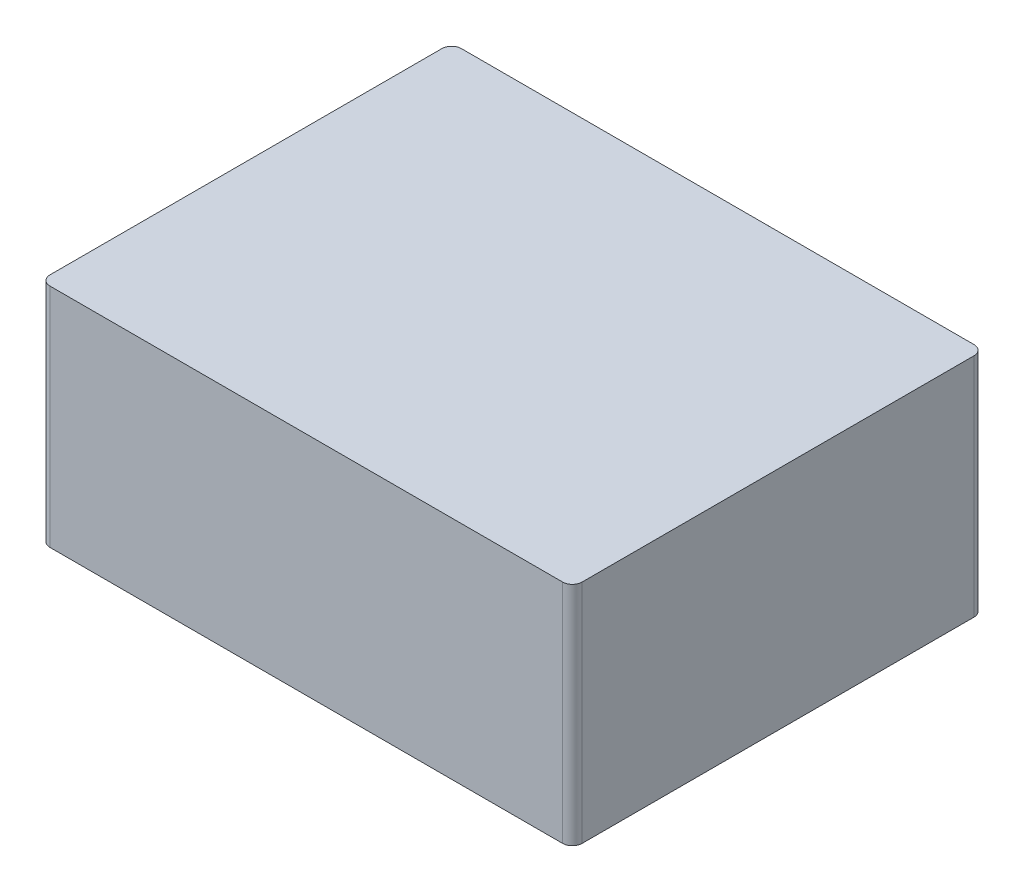
SolidWorks part; units mm, degrees
ref_plane "Front Plane" through (0, 0, 0) normal (0, 0, 1) x (1, 0, 0)
ref_plane "Top Plane" through (0, 0, 0) normal (0, 1, 0) x (1, 0, 0)
ref_plane "Right Plane" through (0, 0, 0) normal (1, 0, 0) x (0, 0, -1)
sketch "Sketch1" plane through (0, 0, 0) normal (0, 1, 0) x (1, 0, 0)
  line L1 (0, 0) -> (109.3, 0)
  line L2 (0, 0) -> (0, 84.5)
  line L3 (0, 84.5) -> (109.3, 84.5)
  line L4 (109.3, 0) -> (109.3, 84.5)
  dimension "D1" = 109.3
  dimension "D2" = 84.5
extrude "Boss-Extrude3" add sketch "Sketch1" along normal blind 46.5
fillet "Fillet2" radius 2 1 edges at (109.3, 23.25, 0)
fillet "Fillet3" radius 2 1 edges at (0, 23.25, 0)
fillet "Fillet4" radius 2 1 edges at (109.3, 23.25, -84.5)
fillet "Fillet5" radius 2 1 edges at (0, 23.25, -84.5)
